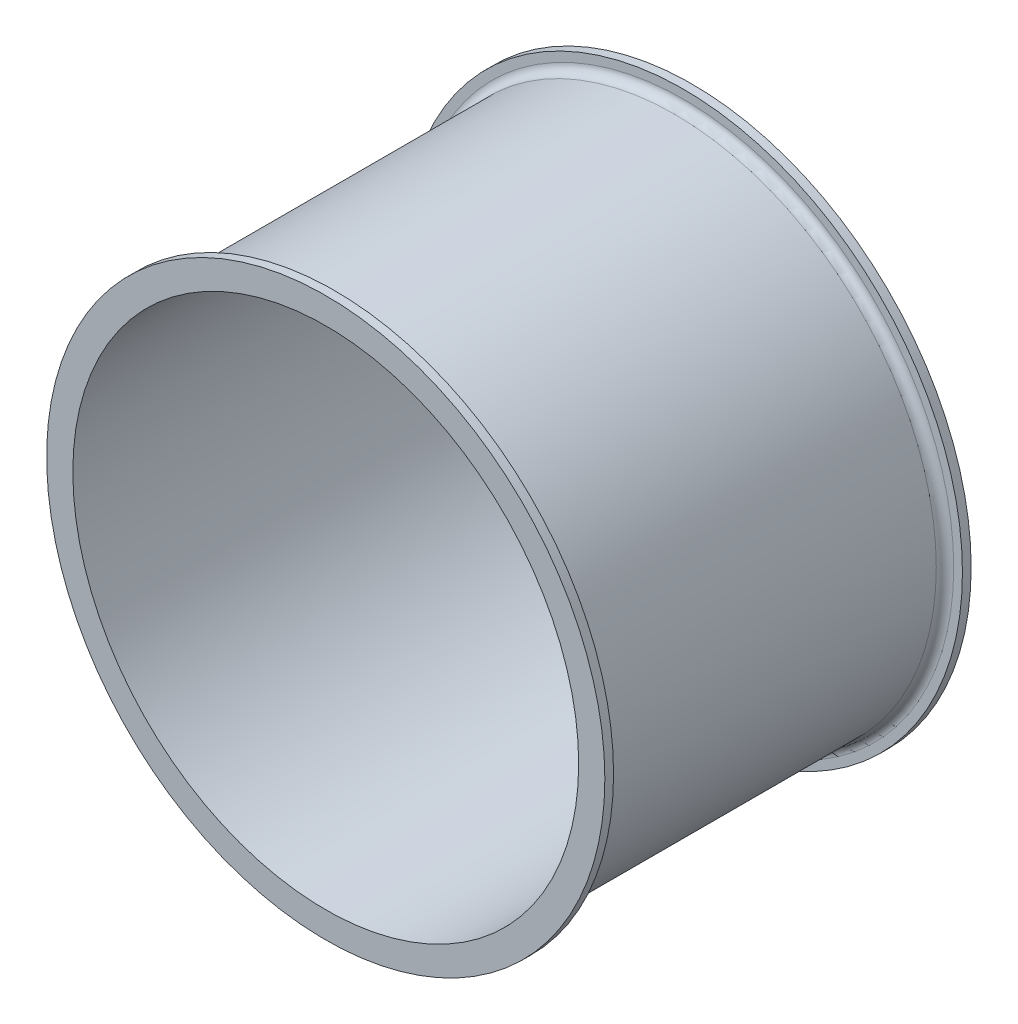
SolidWorks part; units mm, degrees
ref_plane "Ön Düzlem" through (0, 0, 0) normal (0, 0, 1) x (1, 0, 0)
ref_plane "Üst Düzlem" through (0, 0, 0) normal (0, 1, 0) x (1, 0, 0)
ref_plane "Sağ Düzlem" through (0, 0, 0) normal (1, 0, 0) x (0, 0, -1)
sketch "Çizim1" plane through (0, 0, 0) normal (0, 0, 1) x (1, 0, 0)
  circle A0 centre (0, 0) radius 160
extrude "Yükseklik-Ekstrüzyon1" add sketch "Çizim1" along normal blind 5
sketch "Çizim2" plane through (0, 0, 5) normal (0, 0, 1) x (1, 0, 0)
  circle A0 centre (0, 0) radius 150
extrude "Yükseklik-Ekstrüzyon2" add sketch "Çizim2" along normal blind 200
sketch "Çizim3" plane through (0, 0, 205) normal (0, 0, 1) x (1, 0, 0)
  circle A0 centre (0, 0) radius 160
extrude "Yükseklik-Ekstrüzyon3" add sketch "Çizim3" along normal blind 5
sketch "Çizim4" plane through (0, 0, 0) normal (0, 0, -1) x (-1, 0, 0)
  circle A0 centre (0, 0) radius 145
extrude "Kes-Ekstrüzyon1" cut sketch "Çizim4" against normal blind 210
fillet "Radyus1" radius 5 2 edges at (150, 0, 5) (150, 0, 205)
